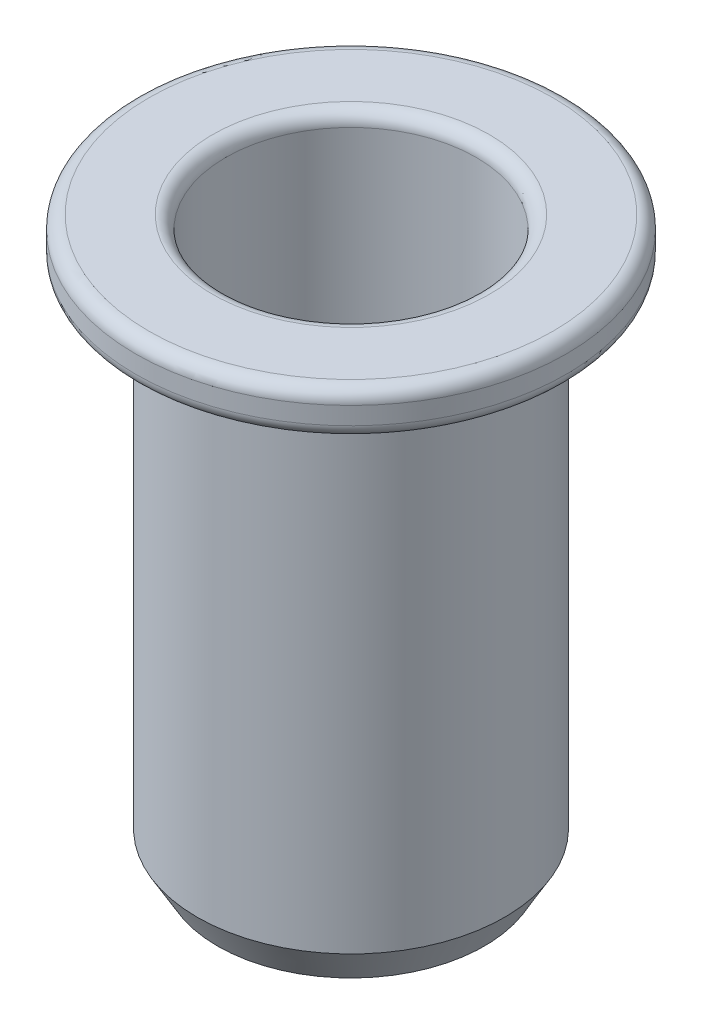
SolidWorks part; units mm, degrees
ref_plane "Front Plane" through (0, 0, 0) normal (0, 0, 1) x (1, 0, 0)
ref_plane "Top Plane" through (0, 0, 0) normal (0, 1, 0) x (1, 0, 0)
ref_plane "Right Plane" through (0, 0, 0) normal (1, 0, 0) x (0, 0, -1)
sketch "Sketch1" plane through (0, 0, 0) normal (0, 0, 1) x (1, 0, 0)
  line L0 (0, 0) -> (0, -4.9017) construction
  line L1 (2.85, 0) -> (4.9, 0)
  line L2 (4.9, 0) -> (4.9, -1)
  line L3 (4.9, -1) -> (3.5, -1)
  line L4 (3.5, -1) -> (3.5, -12.9)
  line L5 (3.5, -12.9) -> (2.5, -12.9)
  line L6 (2.5, -12.9) -> (2.5, -5.7)
  line L7 (2.5, -5.7) -> (2.85, -5.7)
  line L8 (2.85, -5.7) -> (2.85, 0)
  point P10 (2.7016, 0)
  point P13 (2.7016, -0.1679)
  dimension "D1" = 9.8
  dimension "D2" = 5.7
  dimension "D3" = 12.9
  dimension "D4" = 1
  dimension "D5" = 5.7
  dimension "D6" = 5
  dimension "D7" = 7
revolve "Revolve1" add sketch "Sketch1" angle 360 about L0
fillet "Fillet1" radius 0.3 3 edges at (0, -1, 4.9) (0, 0, 4.9) (0, 0, 2.85)
chamfer "Chamfer1" distance 0.8 angle 30 1 edges at (0, -12.9, 3.5)
chamfer "Chamfer2" distance 0.5 angle 30 1 edges at (0, -12.9, 2.5)
